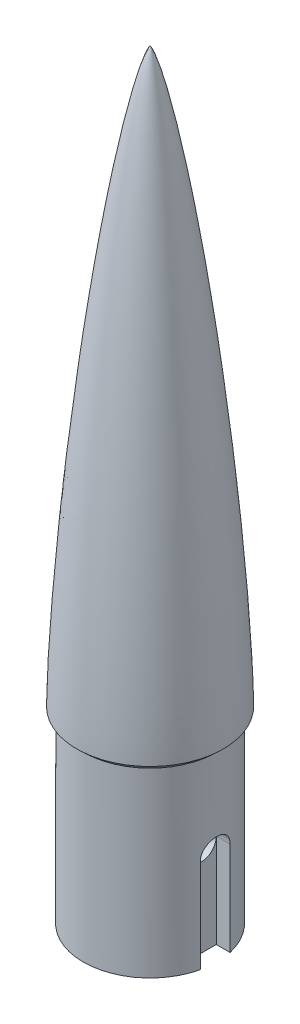
SolidWorks part; units mm, degrees
ref_plane "Front Plane" through (0, 0, 0) normal (0, 0, 1) x (1, 0, 0)
ref_plane "Top Plane" through (0, 0, 0) normal (0, 1, 0) x (1, 0, 0)
ref_plane "Right Plane" through (0, 0, 0) normal (1, 0, 0) x (0, 0, -1)
sketch "Sketch1" plane through (0, 0, 0) normal (0, 1, 0) x (1, 0, 0)
  circle A0 centre (0, 0) radius 8.895
  dimension "D1" = 17.79
extrude "Boss-Extrude1" add sketch "Sketch1" against normal blind 25
sketch "Sketch2" plane through (0, -25, 0) normal (0, -1, 0) x (1, 0, 0)
  line L0 (-6.8312, 1.9844) -> (-6.8312, -1.9844)
  line L1 (-6.8312, 1.9844) -> (-8.6708, 1.9844)
  line L2 (-6.8312, -1.9844) -> (-8.6708, -1.9844)
  line L3 (-8.895, 0) -> (-8.895, -1.1975) construction
  circle A0 centre (0, 0) radius 8.895 construction
  arc A1 (-8.6708, 1.9844) -> (-8.6708, -1.9844) centre (0, 0) ccw
  point P3 (-6.8313, 0)
  dimension "D2" = 3.9688
  dimension "D1" = 2.0637
extrude "Cut-Extrude1" cut sketch "Sketch2" against normal blind 12.5
mirror "Mirror1" about plane through (0, 0, 0) normal (1, 0, 0) of "Cut-Extrude1"
sketch "Sketch3" plane through (0, 0, 0) normal (1, 0, 0) x (0, 0, -1)
  line L0 (1.9844, -12.5) -> (-1.9844, -12.5) construction
  circle A0 centre (0, -12.5) radius 1.9844
extrude "Cut-Extrude2" cut sketch "Sketch3" against normal through all both and the other way through all
sketch "Sketch4" plane through (0, 0, 0) normal (1, 0, 0) x (0, 0, -1)
  line L0 (9.75, 0) -> (0, 0)
  line L1 (8.895, 0) -> (-8.895, 0) construction
  line L2 (0, 0) -> (0, 76.2)
  spline S0 degree 4 poles (0, 76.2) (0.0075, 76.1963) (0.0262, 76.1829) (0.0486, 76.1551) (0.079, 76.1145) (0.1147, 76.0578) (0.161, 75.9772) (0.2302, 75.8413) (0.3375, 75.6032) (0.5088, 75.1694) (0.7807, 74.374) (1.1754, 73.0342) (1.7848, 70.6448) (2.5163, 67.2931) (3.3096, 63.1595) (4.1155, 58.4527) (4.8511, 53.7345) (5.6978, 47.8258) (6.4603, 41.9056) (7.15, 35.9765) (7.7701, 30.0398) (8.2245, 25.2863) (8.6361, 20.5289) (8.9566, 16.363) (9.1998, 12.7899) (9.3789, 9.8108) (9.5063, 7.4266) (9.6105, 5.1571) (9.6812, 3.2428) (9.7258, 1.6841) (9.7429, 0.7218) (9.75, 0.2406) (9.75, 0) knots 0 0 0 0 0 0.000432 0.001199 0.001819 0.002653 0.003898 0.00603 0.009732 0.016211 0.028105 0.049664 0.082236 0.144221 0.206206 0.268191 0.330176 0.392161 0.516132 0.578117 0.640102 0.702087 0.764072 0.826057 0.85705 0.888042 0.919035 0.950027 0.975014 0.987507 1 1 1 1 1 construction
  spline S1 degree 4 poles (0, 76.2) (0.0075, 76.1963) (0.0262, 76.1829) (0.0486, 76.1551) (0.079, 76.1145) (0.1147, 76.0578) (0.161, 75.9772) (0.2302, 75.8413) (0.3375, 75.6032) (0.5088, 75.1694) (0.7807, 74.374) (1.1754, 73.0342) (1.7848, 70.6448) (2.5163, 67.2931) (3.3096, 63.1595) (4.1155, 58.4527) (4.8511, 53.7345) (5.6978, 47.8258) (6.4603, 41.9056) (7.15, 35.9765) (7.7701, 30.0398) (8.2245, 25.2863) (8.6361, 20.5289) (8.9566, 16.363) (9.1998, 12.7899) (9.3789, 9.8108) (9.5063, 7.4266) (9.6105, 5.1571) (9.6812, 3.2428) (9.7258, 1.6841) (9.7429, 0.7218) (9.75, 0.2406) (9.75, 0) knots 0 0 0 0 0 0.000432 0.001199 0.001819 0.002653 0.003898 0.00603 0.009732 0.016211 0.028105 0.049664 0.082236 0.144221 0.206206 0.268191 0.330176 0.392161 0.516132 0.578117 0.640102 0.702087 0.764072 0.826057 0.85705 0.888042 0.919035 0.950027 0.975014 0.987507 1 1 1 1 1
  dimension "D1" = 76.2
  dimension "D2" = 9.75
revolve "Revolve1" add sketch "Sketch4" angle 360 about L2
chamfer "Chamfer1" distance 0.8 angle 45 1 edges at (0, 0, 8.895)
equation "\"D_SHOULDER\"= 17.79mm"
equation "\"OD_AIRF\"= 19mm"
equation "\"W_CORD\"= 3.175mm"
equation "\"L_SHOULDER\"= 25mm"
equation "\"L_CONE\"= 3in"
equation "\"D1@Sketch1\"=\"D_SHOULDER\""
equation "\"D1@Boss-Extrude1\"=\"L_SHOULDER\""
equation "\"D2@Sketch2\"=1.25*\"W_CORD\""
equation "\"D1@Sketch2\"=0.65*\"W_CORD\""
equation "\"D1@Cut-Extrude1\"=\"L_SHOULDER\"/2"
equation "\"D1@Sketch4\"=\"L_CONE\""
